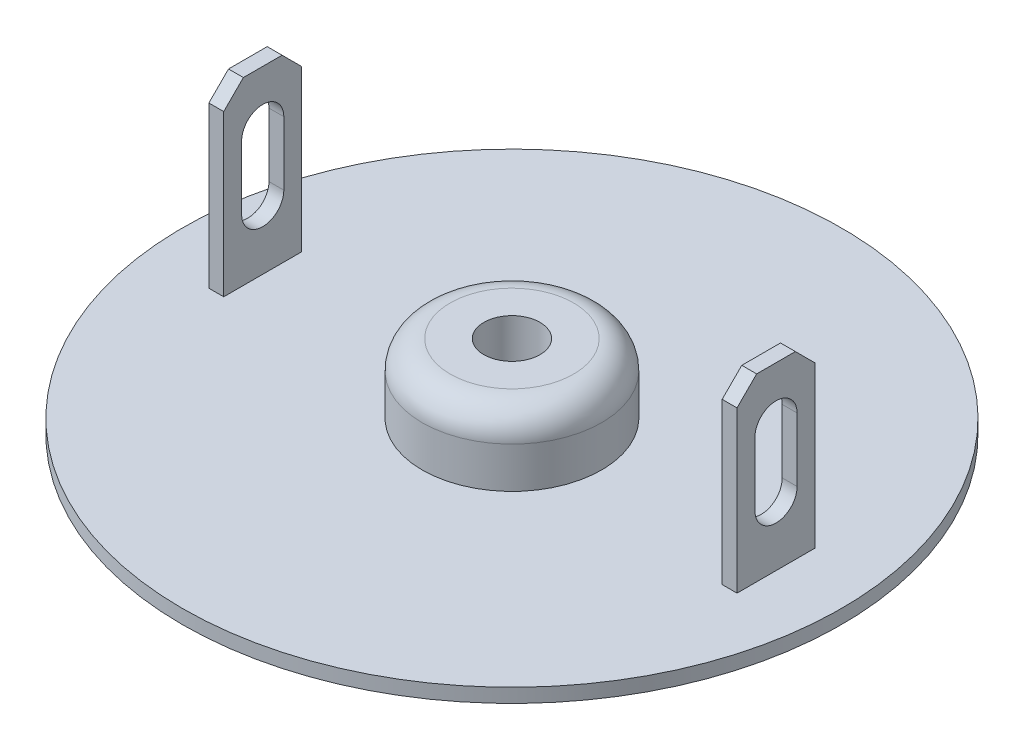
SolidWorks part; units mm, degrees
ref_plane "前视基准面" through (0, 0, 0) normal (0, 0, 1) x (1, 0, 0)
ref_plane "上视基准面" through (0, 0, 0) normal (0, 1, 0) x (1, 0, 0)
ref_plane "右视基准面" through (0, 0, 0) normal (1, 0, 0) x (0, 0, -1)
sketch "草图1" plane through (0, 0, 0) normal (0, 1, 0) x (1, 0, 0)
  circle A0 centre (0, 0) radius 11.75
  circle A1 centre (0, 0) radius 1
  dimension "D1" = 23.5
  dimension "D2" = 2
extrude "凸台-拉伸1" add sketch "草图1" along normal blind 0.5
sketch "草图2" plane through (0, 0.5, 0) normal (0, 1, 0) x (1, 0, 0)
  line L0 (-14.1807, 0) -> (17.5483, 0) construction
  line L5 (0, -12.7693) -> (0, 12.3288) construction
  line L7 (-9.415, -1.39) -> (-8.885, -1.39)
  line L8 (-9.415, -1.39) -> (-9.415, 1.39)
  line L9 (-9.415, 1.39) -> (-8.885, 1.39)
  line L10 (-8.885, -1.39) -> (-8.885, 1.39)
  line L11 (-9.415, -1.39) -> (-8.885, 1.39) construction
  line L12 (-9.415, 1.39) -> (-8.885, -1.39) construction
  point P0 (-9.15, 0)
  dimension "D1" = 0.53
  dimension "D2" = 2.78
  dimension "D3" = 9.15
extrude "凸台-拉伸2" add sketch "草图2" along normal blind 6.42
chamfer "倒角1" distance 0.7 angle 45 2 edges at (-9.15, 6.92, -1.39) (-9.15, 6.92, 1.39)
sketch "草图3" plane through (-9.415, 0, 0) normal (-1, 0, 0) x (0, 0, 1)
  line L0 (0, 4.992) -> (0, 2.7224) construction
  line L1 (0.7519, 4.992) -> (0.7519, 2.7224)
  line L2 (-0.7519, 4.992) -> (-0.7519, 2.7224)
  arc A0 (0.7519, 4.992) -> (-0.7519, 4.992) centre (0, 4.992) ccw
  arc A1 (-0.7519, 2.7224) -> (0.7519, 2.7224) centre (0, 2.7224) ccw
  point P3 (0, 3.8572)
extrude "切除-拉伸1" cut sketch "草图3" against normal up to next (0.53 mm away)
sketch "草图4" plane through (0, 0, 0) normal (0, 0, 1) x (1, 0, 0)
  line L0 (0, 3.4957) -> (0, -1.6123) construction
  line L1 (-1, 0.5) -> (-3.2, 0.5)
  line L2 (-1, 0.5) -> (-1, 2.96)
  line L3 (-1, 2.96) -> (-3.2, 2.96)
  line L4 (-3.2, 0.5) -> (-3.2, 2.96)
  dimension "D1" = 3.2
  dimension "D2" = 2.46
revolve "旋转1" add sketch "草图4" angle 360 about L0
fillet "圆角1" radius 1 1 edges at (0, 2.96, 3.2)
mirror "镜向1" about plane through (0, 0, 0) normal (1, 0, 0) of "切除-拉伸1", "倒角1", "凸台-拉伸2"
